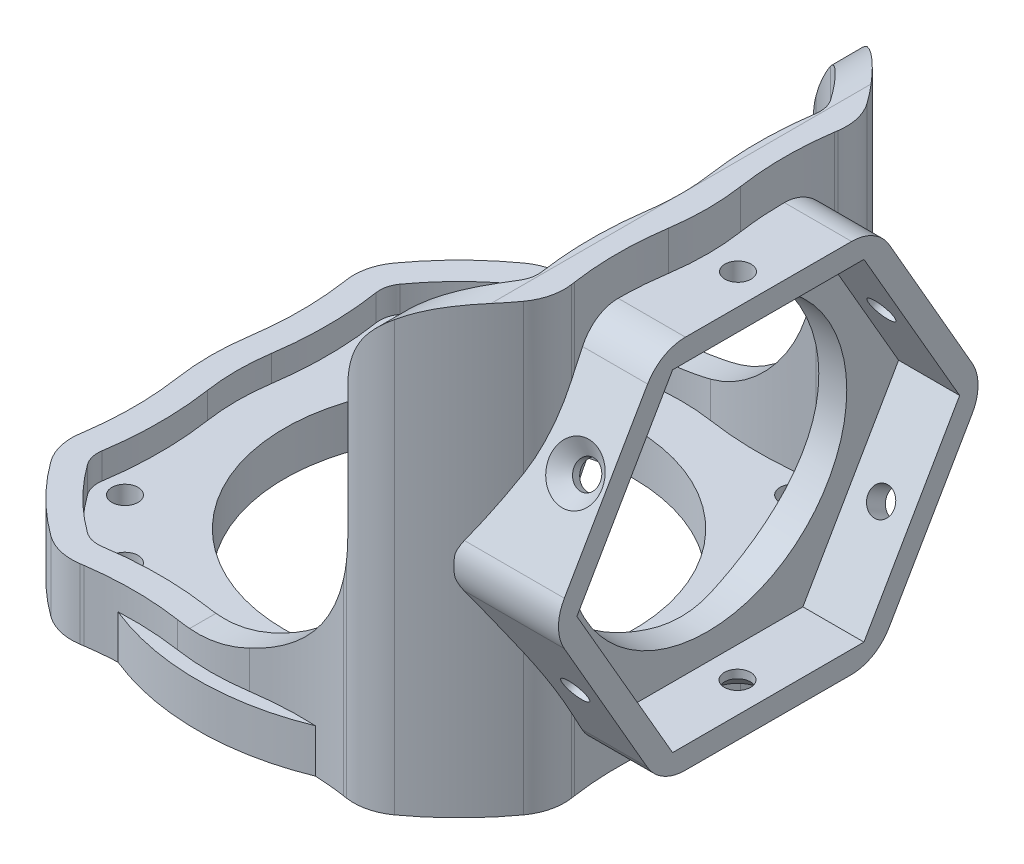
SolidWorks part; units mm, degrees
material "6061 合金"
ref_plane "前视基准面" through (0, 0, 0) normal (0, 0, 1) x (1, 0, 0)
ref_plane "上视基准面" through (0, 0, 0) normal (0, 1, 0) x (1, 0, 0)
ref_plane "右视基准面" through (0, 0, 0) normal (1, 0, 0) x (0, 0, -1)
sketch "草图1" plane through (0, 0, 0) normal (0, 1, 0) x (1, 0, 0)
  line L0 (0, 0) -> (0, 46.6195) construction
  line L1 (0, 0) -> (-41.7463, 0) construction
  line L2 (-22.5267, 15.7734) -> (0, 0) construction
  line L3 (-15.7734, 22.5267) -> (0, 0) construction
  circle A0 centre (0, 0) radius 30
  circle A1 centre (0, 0) radius 20
  circle A2 centre (0, 0) radius 27.5 construction
  circle A3 centre (-22.5267, 15.7734) radius 1.5
  circle A4 centre (-15.7734, 22.5267) radius 1.5
  circle A5 centre (22.5267, 15.7734) radius 1.5
  circle A6 centre (15.7734, 22.5267) radius 1.5
  circle A7 centre (22.5267, -15.7734) radius 1.5
  circle A8 centre (15.7734, -22.5267) radius 1.5
  circle A9 centre (-22.5267, -15.7734) radius 1.5
  circle A10 centre (-15.7734, -22.5267) radius 1.5
  dimension "D1" = 60
  dimension "D2" = 40
  dimension "D3" = 55
  dimension "D5" = 3
  dimension "D4" = 35
  dimension "D6" = 35
extrude "凸台-拉伸1" add sketch "草图1" along normal blind 5
sketch "草图2" plane through (0, 5, 0) normal (0, 1, 0) x (1, 0, 0)
  line L0 (0, 0) -> (39.9587, 0) construction
  line L1 (0, 0) -> (0, -36.8515) construction
  line L2 (0, 0) -> (21.5668, 21.5668) construction
  arc A0 (24.7368, -3.2548) -> (24.949, 0.2177) centre (0, 0) ccw construction
  arc A1 (25.1774, -3.6784) -> (25.1774, 3.6784) centre (0.5, 0) ccw
  arc A2 (24.949, 0.2177) -> (24.6762, 3.686) centre (0, 0) ccw construction
  arc A3 (25.1774, 3.6784) -> (24.7671, 8.11) centre (64.7402, 9.5757) cw
  arc A4 (24.2388, 9.2464) -> (24.6762, 3.686) centre (64.2373, 9.5955) ccw construction
  arc A5 (24.7671, 8.11) -> (25.2125, 15.7044) centre (64.7402, 9.5757) cw
  arc A6 (24.7179, 15.7777) -> (24.2388, 9.2464) centre (64.2373, 9.5955) ccw construction
  arc A7 (25.2125, 15.7044) -> (24.675, 17.9275) centre (22.248, 16.1641) ccw
  arc A8 (24.7179, 15.7777) -> (24.2705, 17.6336) centre (22.248, 16.1641) ccw construction
  arc A9 (24.675, 17.9275) -> (17.9275, 24.675) centre (0, 0) ccw
  circle A10 centre (0, 0) radius 30 construction
  arc A11 (28.1446, 4.1207) -> (28.1446, -4.1207) centre (0.5, 0) cw
  arc A12 (28.1446, 4.1207) -> (28.1241, 14.8917) centre (64.7402, 9.5757) cw
  arc A13 (28.1241, 14.8917) -> (28.1806, 15.2677) centre (65.7457, 9.4297) cw
  arc A14 (28.1806, 15.2677) -> (27.1021, 19.6908) centre (22.248, 16.1641) ccw
  arc A15 (19.6908, 27.1021) -> (27.1021, 19.6908) centre (0, 0) cw
  arc A16 (15.2677, 28.1806) -> (19.6908, 27.1021) centre (16.1641, 22.248) cw
  arc A17 (14.8917, 28.1241) -> (15.2677, 28.1806) centre (9.4297, 65.7457) ccw
  arc A18 (4.1207, 28.1446) -> (14.8917, 28.1241) centre (9.5757, 64.7402) ccw
  arc A19 (4.1207, 28.1446) -> (-4.1207, 28.1446) centre (0, 0.5) ccw
  arc A20 (15.7044, 25.2125) -> (17.9275, 24.675) centre (16.1641, 22.248) cw
  arc A21 (8.11, 24.7671) -> (15.7044, 25.2125) centre (9.5757, 64.7402) ccw
  arc A22 (3.6784, 25.1774) -> (8.11, 24.7671) centre (9.5757, 64.7402) ccw
  arc A23 (-3.6784, 25.1774) -> (3.6784, 25.1774) centre (0, 0.5) cw
  arc A24 (-3.6784, 25.1774) -> (-8.11, 24.7671) centre (-9.5757, 64.7402) cw
  arc A25 (-8.11, 24.7671) -> (-15.7044, 25.2125) centre (-9.5757, 64.7402) cw
  arc A26 (-15.7044, 25.2125) -> (-17.9275, 24.675) centre (-16.1641, 22.248) ccw
  arc A27 (-4.1207, 28.1446) -> (-14.8917, 28.1241) centre (-9.5757, 64.7402) cw
  arc A28 (-14.8917, 28.1241) -> (-15.2677, 28.1806) centre (-9.4297, 65.7457) cw
  arc A29 (-15.2677, 28.1806) -> (-19.6908, 27.1021) centre (-16.1641, 22.248) ccw
  arc A30 (-19.6908, 27.1021) -> (-27.1021, 19.6908) centre (0, 0) ccw
  arc A31 (-28.1806, 15.2677) -> (-27.1021, 19.6908) centre (-22.248, 16.1641) cw
  arc A32 (-28.1241, 14.8917) -> (-28.1806, 15.2677) centre (-65.7457, 9.4297) ccw
  arc A33 (-28.1446, 4.1207) -> (-28.1241, 14.8917) centre (-64.7402, 9.5757) ccw
  arc A34 (-28.1446, 4.1207) -> (-28.1446, -4.1207) centre (-0.5, 0) ccw
  arc A35 (-24.675, 17.9275) -> (-17.9275, 24.675) centre (0, 0) cw
  arc A36 (-25.2125, 15.7044) -> (-24.675, 17.9275) centre (-22.248, 16.1641) cw
  arc A37 (-24.7671, 8.11) -> (-25.2125, 15.7044) centre (-64.7402, 9.5757) ccw
  arc A38 (-25.1774, 3.6784) -> (-24.7671, 8.11) centre (-64.7402, 9.5757) ccw
  arc A39 (-25.1774, -3.6784) -> (-25.1774, 3.6784) centre (-0.5, 0) cw
  arc A40 (-25.1774, -3.6784) -> (-24.7671, -8.11) centre (-64.7402, -9.5757) cw
  arc A41 (-24.7671, -8.11) -> (-25.2125, -15.7044) centre (-64.7402, -9.5757) cw
  arc A42 (-25.2125, -15.7044) -> (-24.675, -17.9275) centre (-22.248, -16.1641) ccw
  arc A43 (-24.675, -17.9275) -> (-17.9275, -24.675) centre (0, 0) ccw
  arc A44 (-28.1446, -4.1207) -> (-28.1241, -14.8917) centre (-64.7402, -9.5757) cw
  arc A45 (-28.1241, -14.8917) -> (-28.1806, -15.2677) centre (-65.7457, -9.4297) cw
  arc A46 (-28.1806, -15.2677) -> (-27.1021, -19.6908) centre (-22.248, -16.1641) ccw
  arc A47 (-19.6908, -27.1021) -> (-27.1021, -19.6908) centre (0, 0) cw
  arc A48 (-15.2677, -28.1806) -> (-19.6908, -27.1021) centre (-16.1641, -22.248) cw
  arc A49 (-14.8917, -28.1241) -> (-15.2677, -28.1806) centre (-9.4297, -65.7457) ccw
  arc A50 (-4.1207, -28.1446) -> (-14.8917, -28.1241) centre (-9.5757, -64.7402) ccw
  arc A51 (-15.7044, -25.2125) -> (-17.9275, -24.675) centre (-16.1641, -22.248) cw
  arc A52 (-8.11, -24.7671) -> (-15.7044, -25.2125) centre (-9.5757, -64.7402) ccw
  arc A53 (-3.6784, -25.1774) -> (-8.11, -24.7671) centre (-9.5757, -64.7402) ccw
  arc A54 (-3.6784, -25.1774) -> (3.6784, -25.1774) centre (0, -0.5) ccw
  arc A55 (3.6784, -25.1774) -> (8.11, -24.7671) centre (9.5757, -64.7402) cw
  arc A56 (8.11, -24.7671) -> (15.7044, -25.2125) centre (9.5757, -64.7402) cw
  arc A57 (15.7044, -25.2125) -> (17.9275, -24.675) centre (16.1641, -22.248) ccw
  arc A58 (4.1207, -28.1446) -> (-4.1207, -28.1446) centre (0, -0.5) cw
  arc A59 (4.1207, -28.1446) -> (14.8917, -28.1241) centre (9.5757, -64.7402) cw
  arc A60 (14.8917, -28.1241) -> (15.2677, -28.1806) centre (9.4297, -65.7457) cw
  arc A61 (15.2677, -28.1806) -> (19.6908, -27.1021) centre (16.1641, -22.248) ccw
  arc A62 (19.6908, -27.1021) -> (27.1021, -19.6908) centre (0, 0) ccw
  arc A63 (28.1806, -15.2677) -> (27.1021, -19.6908) centre (22.248, -16.1641) cw
  arc A64 (28.1241, -14.8917) -> (28.1806, -15.2677) centre (65.7457, -9.4297) ccw
  arc A65 (28.1446, -4.1207) -> (28.1241, -14.8917) centre (64.7402, -9.5757) ccw
  arc A66 (24.675, -17.9275) -> (17.9275, -24.675) centre (0, 0) cw
  arc A67 (25.2125, -15.7044) -> (24.675, -17.9275) centre (22.248, -16.1641) cw
  arc A68 (24.7671, -8.11) -> (25.2125, -15.7044) centre (64.7402, -9.5757) ccw
  arc A69 (25.1774, -3.6784) -> (24.7671, -8.11) centre (64.7402, -9.5757) ccw
  point P7 (24.95, 0)
  point P9 (25.45, 0)
  point P13 (0, -24.95)
  point P60 (0, 25.45)
  point P61 (0, 24.95)
  point P85 (-25.45, 0)
  point P86 (-24.95, 0)
  point P129 (0, -25.45)
  dimension "D2" = 30.5
  dimension "D1" = 0.5
extrude "凸台-拉伸2" add sketch "草图2" along normal blind 46 and the other way blind 5
sketch "草图3" plane through (0, 0, 0) normal (0, 0, 1) x (1, 0, 0)
  line L0 (-30.7273, 8) -> (-30.7273, -1.7514)
  line L2 (-30.7273, -1.7514) -> (-34.3096, -1.7514)
  line L3 (-34.3096, -1.7514) -> (-34.3096, 55.8818)
  line L4 (-34.3096, 55.8818) -> (36.2257, 55.8818)
  line L5 (36.2257, 55.8818) -> (36.2257, -1.7514)
  line L6 (36.2257, -1.7514) -> (28.45, -1.7514)
  line L7 (28.45, -1.7514) -> (28.45, 51)
  line L8 (28.45, 5) -> (28.45, 51) construction
  line L9 (28.45, 51) -> (25.45, 51)
  line L10 (14.8917, 51) -> (4.1207, 51) construction
  line L11 (15.45, 41) -> (15.45, 26)
  line L12 (-2.55, 8) -> (-30.7273, 8)
  line L13 (-27.7815, 5) -> (-30, 5) construction
  arc A0 (15.45, 26) -> (-2.55, 8) centre (-2.55, 26) cw
  arc A1 (25.45, 51) -> (15.45, 41) centre (25.45, 41) ccw
  point P20 (15.45, 51)
  dimension "D1" = 18
  dimension "D2" = 10
  dimension "D3" = 3
  dimension "D4" = 3
extrude "切除-拉伸1" cut sketch "草图3" along normal through all and the other way through all
sketch "草图4" plane through (28.45, 0, 0) normal (1, 0, 0) x (0, 0, -1)
  line L0 (0, 0) -> (0, 56.7093) construction
  line L1 (28.1446, 5) -> (27.7402, 5) construction
  circle A2 centre (0, 25) radius 20 construction
  circle A3 centre (0, 25) radius 16
  dimension "D1" = 40
  dimension "D2" = 32
extrude "切除-拉伸2" cut sketch "草图4" against normal blind 22 and the other way blind 19
sketch "草图5" plane through (28.45, 0, 0) normal (1, 0, 0) x (0, 0, -1)
  line L1 (13.8308, 5.9813) -> (23.3793, 22.4685)
  line L2 (23.386, 27.4685) -> (13.882, 43.9813)
  line L3 (9.5553, 46.4871) -> (-9.4973, 46.5128)
  line L4 (-13.8308, 44.0187) -> (-23.3793, 27.5315)
  line L5 (-23.386, 22.5315) -> (-13.882, 6.0187)
  line L6 (-9.5553, 3.5129) -> (9.4973, 3.4872)
  circle A0 centre (0, 25) radius 16
  arc A1 (-4.1207, 40.4603) -> (-14.8917, 30.8513) centre (0, 25) ccw construction
  circle A2 centre (0, 25) radius 22.5 construction
  circle A3 centre (0, 25) radius 21.5 construction
  arc A4 (13.882, 43.9813) -> (9.5553, 46.4871) centre (9.5485, 41.4871) ccw
  arc A5 (23.3793, 22.4685) -> (23.386, 27.4685) centre (19.0525, 24.9743) ccw
  arc A6 (13.8308, 5.9813) -> (9.4973, 3.4872) centre (9.504, 8.4872) cw
  arc A7 (-13.882, 6.0187) -> (-9.5553, 3.5129) centre (-9.5485, 8.5129) ccw
  arc A8 (-23.3793, 27.5315) -> (-23.386, 22.5315) centre (-19.0525, 25.0257) ccw
  arc A9 (-9.4973, 46.5128) -> (-13.8308, 44.0187) centre (-9.504, 41.5128) ccw
  dimension "D1" = 45
  dimension "D2" = 43
  dimension "D3" = 5
sketch "草图7" plane through (0, 51, 0) normal (0, 1, 0) x (1, 0, 0)
  line L0 (28.1241, -14.8917) -> (31.1027, -14.0835)
  line L1 (31.1027, -14.0835) -> (31.1027, 14.2516)
  line L2 (31.1027, 14.2516) -> (28.1241, 14.8917)
  arc A0 (28.1241, -14.8917) -> (28.1446, -4.1207) centre (64.7402, -9.5757) cw
  arc A1 (28.1446, -4.1207) -> (28.1241, -14.8917) centre (64.7402, -9.5757) ccw construction
  arc A2 (28.1446, -4.1207) -> (28.1446, 4.1207) centre (0.5, 0) ccw
  arc A3 (28.1446, 4.1207) -> (28.1241, 14.8917) centre (64.7402, 9.5757) cw
extrude "切除-拉伸3" cut sketch "草图7" against normal through all
extrude "凸台-拉伸4" add sketch "草图5" along normal blind 7 and the other way blind 5
sketch "草图8" plane through (0, 51, 0) normal (0, 1, 0) x (1, 0, 0)
  line L0 (17.9275, -24.675) -> (17.9275, 24.675)
  arc A0 (17.9275, -24.675) -> (24.675, -17.9275) centre (0, 0) ccw
  arc A1 (24.675, -17.9275) -> (25.2125, -15.7044) centre (22.248, -16.1641) ccw
  arc A2 (25.2125, -15.7044) -> (25.1774, -3.6784) centre (64.7402, -9.5757) cw
  arc A3 (25.1774, -3.6784) -> (25.45, 0) centre (0.5, 0) ccw
  arc A4 (25.45, 0) -> (25.1774, 3.6784) centre (0.5, 0) ccw
  arc A5 (25.1774, 3.6784) -> (25.2125, 15.7044) centre (64.7403, 9.5757) cw
  arc A6 (25.2125, 15.7044) -> (24.675, 17.9275) centre (22.248, 16.1641) ccw
  arc A7 (24.675, 17.9275) -> (17.9275, 24.675) centre (0, 0) ccw
extrude "切除-拉伸4" cut sketch "草图8" against normal up to surface (46 mm away) up to face at (0, 5, 28.5061)
sketch "草图9" plane through (35.45, 0, 0) normal (1, 0, 0) x (0, 0, -1)
  line L1 (10.9697, 6) -> (21.9393, 25)
  line L2 (21.9393, 25) -> (10.9697, 44)
  line L3 (10.9697, 44) -> (-10.9697, 44)
  line L4 (-10.9697, 44) -> (-21.9393, 25)
  line L5 (-21.9393, 25) -> (-10.9697, 6)
  line L6 (-10.9697, 6) -> (10.9697, 6)
  circle A2 centre (0, 25) radius 19 construction
  dimension "D2" = 38
extrude "切除-拉伸5" cut sketch "草图9" against normal blind 7
sketch "草图10" plane through (0, 17.0543, 29.4472) normal (0, 0.5012, 0.8654) x (1, 0, 0)
  line L0 (35.45, 21.6338) -> (31.95, 21.6338) construction
  line L1 (35.45, 31.16) -> (35.45, 12.1075) construction
  circle A0 centre (31.95, 21.6338) radius 1.5
  circle A1 centre (31.95, 21.6338) radius 3 construction
  dimension "D2" = 3
  dimension "D3" = 6
  dimension "D1" = 3.5
sketch "草图11" plane through (0, -4.5041, 7.8256) normal (0, -0.4988, 0.8667) x (1, 0, 0)
  line L0 (35.45, 21.6675) -> (31.95, 21.6675) construction
  line L1 (35.45, 31.1937) -> (35.45, 12.1412) construction
  circle A0 centre (31.95, 21.6675) radius 1.5
  circle A1 centre (31.95, 21.6675) radius 3 construction
  dimension "D1" = 6
  dimension "D2" = 3
  dimension "D3" = 3.5
extrude "切除-拉伸6" cut sketch "草图10" against normal through all
extrude "切除-拉伸7" cut sketch "草图11" against normal through all
sketch "草图12" plane through (0, 3.5, -0.0047) normal (0, -1, 0.0013) x (1, 0, 0)
  line L0 (35.45, 0.0337) -> (31.95, 0.0337) construction
  line L1 (35.45, 9.56) -> (35.45, -9.4926) construction
  circle A0 centre (31.95, 0.0337) radius 1.5
  circle A1 centre (31.95, 0.0337) radius 3 construction
  dimension "D2" = 3
  dimension "D3" = 6
  dimension "D1" = 3.5
extrude "切除-拉伸8" cut sketch "草图12" against normal through all
sketch "草图13" plane through (0, 0, 0) normal (0, -1, 0) x (1, 0, 0)
  line L0 (-14.0904, 25.6743) -> (-15.604, 24.7943)
  line L1 (-15.604, 24.7943) -> (-17.3639, 24.0199)
  line L2 (-17.3639, 24.0199) -> (-20.8838, 20.4649)
  line L3 (-20.8838, 20.4649) -> (-23.9813, 16.8394)
  line L4 (-23.9813, 16.8394) -> (-26.0197, 14.4535)
  line L5 (-26.0197, 14.4535) -> (-25.5653, 18.6521)
  line L6 (-25.5653, 18.6521) -> (-20.8838, 24.1315)
  line L7 (-20.8838, 24.1315) -> (-17.2837, 26.2246)
  line L8 (-17.2837, 26.2246) -> (-14.0904, 25.6743)
  line L9 (-21.4676, -19.5744) -> (-18.6381, -22.3759)
  line L10 (-18.6381, -22.3759) -> (-16.3467, -24.3337)
  line L11 (-16.3467, -24.3337) -> (-15.3102, -25.612)
  line L12 (-15.3102, -25.612) -> (-16.3467, -26.4523)
  line L13 (-16.3467, -26.4523) -> (-20.653, -24.0308)
  line L14 (-20.653, -24.0308) -> (-24.3427, -20.1015)
  line L15 (-24.3427, -20.1015) -> (-25.7925, -17.6078)
  line L16 (-25.7925, -17.6078) -> (-26.0197, -15.2619)
  line L17 (-26.0197, -15.2619) -> (-25.0137, -15.4353)
  line L18 (-25.0137, -15.4353) -> (-23.3178, -17.8374)
  line L19 (-23.3178, -17.8374) -> (-21.4676, -19.5744)
  line L20 (23.7623, -17.4526) -> (24.8079, -16.1747)
  line L21 (24.8079, -16.1747) -> (25.9115, -15.6326)
  line L22 (25.9115, -15.6326) -> (26.2407, -17.1234)
  line L23 (26.2407, -17.1234) -> (25.0402, -19.4275)
  line L24 (25.0402, -19.4275) -> (22.5619, -22.0027)
  line L25 (22.5619, -22.0027) -> (19.2897, -24.4617)
  line L26 (19.2897, -24.4617) -> (16.7339, -25.9913)
  line L27 (16.7339, -25.9913) -> (14.7396, -25.7589)
  line L28 (14.7396, -25.7589) -> (15.3397, -24.6072)
  line L29 (15.3397, -24.6072) -> (16.9544, -24.0987)
  line L30 (16.9544, -24.0987) -> (18.775, -22.207)
  line L31 (18.775, -22.207) -> (22.5619, -18.9047)
  line L32 (22.5619, -18.9047) -> (23.7623, -17.4526)
  line L33 (14.9976, 25.5005) -> (16.9544, 24.4377)
  line L34 (16.9544, 24.4377) -> (19.002, 22.7487)
  line L35 (19.002, 22.7487) -> (20.71, 20.718)
  line L36 (20.71, 20.718) -> (22.5619, 19.01)
  line L37 (22.5619, 19.01) -> (24.0501, 16.8394)
  line L38 (24.0501, 16.8394) -> (25.8018, 15.2238)
  line L39 (25.8018, 15.2238) -> (26.0618, 16.5239)
  line L40 (26.0618, 16.5239) -> (24.2428, 19.2523)
  line L41 (24.2428, 19.2523) -> (22.3922, 21.4524)
  line L42 (22.3922, 21.4524) -> (19.856, 23.7916)
  line L43 (19.856, 23.7916) -> (17.8147, 25.6743)
  line L44 (17.8147, 25.6743) -> (15.976, 26.2246)
  line L45 (15.976, 26.2246) -> (14.9976, 25.5005)
extrude "凸台-拉伸5" add sketch "草图13" against normal up to surface (5 mm away) up to face at (0, 5, 28.5061)
chamfer "倒角1" distance 1.55 angle 45 11 edges at (31.95, 37.0249, -17.8858) (31.95, 34.4771, 19.3568) (31.95, 3.498, -1.471) (22.5267, 0, -17.2734) (15.7734, 0, -24.0267) (22.5267, 0, 17.2734) (15.7734, 0, 24.0267) (-15.7734, 0, 21.0267) (-22.5267, 0, 14.2734) (-15.7734, 0, -21.0267) (-22.5267, 0, -14.2734)
